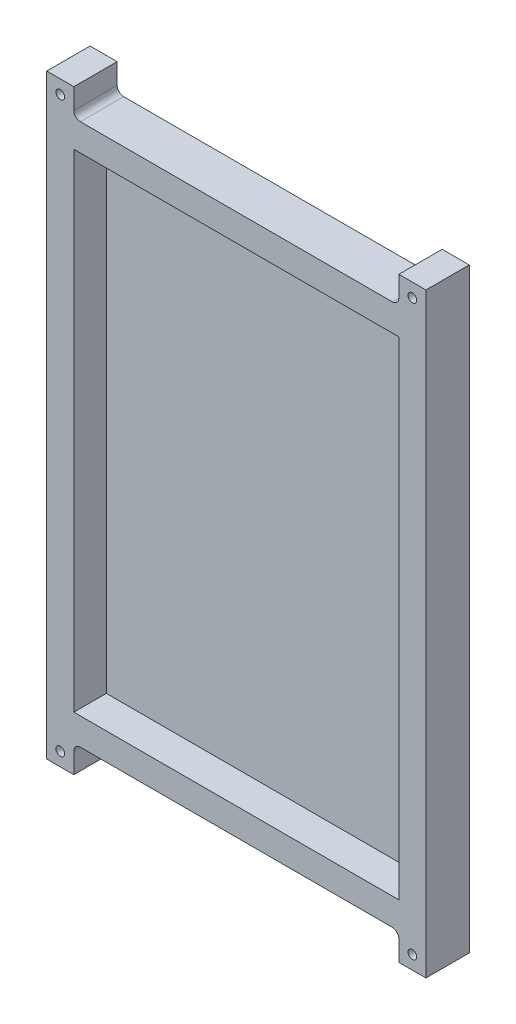
SolidWorks part; units mm, degrees
ref_plane "Ön Düzlem" through (0, 0, 0) normal (1, 0, 0) x (0, 1, 0)
ref_plane "Üst Düzlem" through (0, 0, 0) normal (0, 0, 1) x (0, 1, 0)
ref_plane "Sağ Düzlem" through (0, 0, 0) normal (0, 1, 0) x (-1, 0, 0)
sketch "Sketch1" plane through (0, 0, 0) normal (0, 0, 1) x (0, 1, 0)
  line L0 (-10, 2.4) -> (-10, 117.6)
  line L1 (0, 0) -> (180, 0) construction
  line L2 (0, 0) -> (0, 120) construction
  line L3 (0, 120) -> (180, 120) construction
  line L4 (180, 0) -> (180, 120) construction
  line L5 (-10, 130) -> (190, 130)
  line L6 (190, 2.4) -> (190, 117.6)
  line L7 (-10, -10) -> (190, -10)
  line L8 (-10, -10) -> (-10, 130) construction
  line L9 (-10, 130) -> (-20, 130)
  line L11 (-12.4, 120) -> (-20, 120)
  line L12 (-20, 130) -> (-20, 120)
  line L13 (-10, -10) -> (-20, -10)
  line L15 (-12.4, 0) -> (-20, 0)
  line L16 (-20, -10) -> (-20, 0)
  line L17 (190, -10) -> (200, -10)
  line L19 (192.4, 0) -> (200, 0)
  line L20 (200, -10) -> (200, 0)
  line L21 (190, 130) -> (200, 130)
  line L23 (192.4, 120) -> (200, 120)
  line L24 (200, 130) -> (200, 120)
  line L25 (190, -10) -> (190, 130) construction
  arc A0 (190, 117.6) -> (192.4, 120) centre (192.4, 117.6) cw
  arc A1 (190, 2.4) -> (192.4, 0) centre (192.4, 2.4) ccw
  arc A2 (-10, 2.4) -> (-12.4, 0) centre (-12.4, 2.4) cw
  arc A3 (-10, 117.6) -> (-12.4, 120) centre (-12.4, 117.6) ccw
  point P23 (190, 120)
  point P26 (190, 0)
  point P29 (-10, 0)
  point P32 (-10, 120)
  dimension "D8" = 2.4
  dimension "D1" = 120
  dimension "D2" = 180
  dimension "D4" = 10
  dimension "D5" = 10
  dimension "D6" = 10
  dimension "D7" = 10
  dimension "D3" = 10
extrude "Boss-Extrude1" add sketch "Sketch1" along normal blind 4
sketch "Sketch2" plane through (0, 0, 4) normal (0, 0, 1) x (1, 0, 0)
  line L27 (10, -20) -> (10, 200)
  line L28 (10, 200) -> (0, 200)
  line L29 (0, 200) -> (0, 192.4)
  line L30 (-2.4, 190) -> (-117.6, 190)
  line L31 (-120, 192.4) -> (-120, 200)
  line L32 (-120, 200) -> (-130, 200)
  line L33 (-130, 200) -> (-130, -20)
  line L34 (-130, -20) -> (-120, -20)
  line L35 (-120, -20) -> (-120, -12.4)
  line L36 (-117.6, -10) -> (-2.4, -10)
  line L37 (0, -12.4) -> (0, -20)
  line L38 (0, -20) -> (10, -20)
  line L39 (10, -20) -> (10, 200)
  line L40 (10, 200) -> (0, 200)
  line L41 (0, 200) -> (0, 192.4)
  line L42 (-2.4, 190) -> (-117.6, 190)
  line L43 (-120, 192.4) -> (-120, 200)
  line L44 (-120, 200) -> (-130, 200)
  line L45 (-130, 200) -> (-130, -20)
  line L46 (-130, -20) -> (-120, -20)
  line L47 (-120, -20) -> (-120, -12.4)
  line L48 (-117.6, -10) -> (-2.4, -10)
  line L49 (0, -12.4) -> (0, -20)
  line L50 (0, -20) -> (10, -20)
  line L51 (-120, 0) -> (0, 0)
  line L52 (0, 0) -> (0, 180)
  line L53 (-120, 180) -> (-120, 0)
  line L54 (0, 180) -> (-120, 180)
  line L55 (-120, 0) -> (0, 0)
  line L56 (0, 0) -> (0, 180)
  line L57 (-120, 180) -> (-120, 0)
  line L58 (0, 180) -> (-120, 180)
  arc A8 (-2.4, 190) -> (0, 192.4) centre (-2.4, 192.4) ccw
  arc A9 (-120, 192.4) -> (-117.6, 190) centre (-117.6, 192.4) ccw
  arc A10 (-117.6, -10) -> (-120, -12.4) centre (-117.6, -12.4) ccw
  arc A11 (0, -12.4) -> (-2.4, -10) centre (-2.4, -12.4) ccw
  arc A12 (-2.4, 190) -> (0, 192.4) centre (-2.4, 192.4) ccw
  arc A13 (-120, 192.4) -> (-117.6, 190) centre (-117.6, 192.4) ccw
  arc A14 (-117.6, -10) -> (-120, -12.4) centre (-117.6, -12.4) ccw
  arc A15 (0, -12.4) -> (-2.4, -10) centre (-2.4, -12.4) ccw
  dimension "D1" = 0
  dimension "D2" = 0
extrude "Boss-Extrude2" add sketch "Sketch2" along normal blind 12
sketch "Sketch3" plane through (0, 0, 16) normal (0, 0, 1) x (1, 0, 0)
  circle A0 centre (-125, 195) radius 1.6
  circle A1 centre (5, 195) radius 1.6
  circle A2 centre (5, -15) radius 1.6
  circle A3 centre (-125, -15) radius 1.6
  point P6 (0, 0)
extrude "Cut-Extrude1" cut sketch "Sketch3" against normal blind 12
